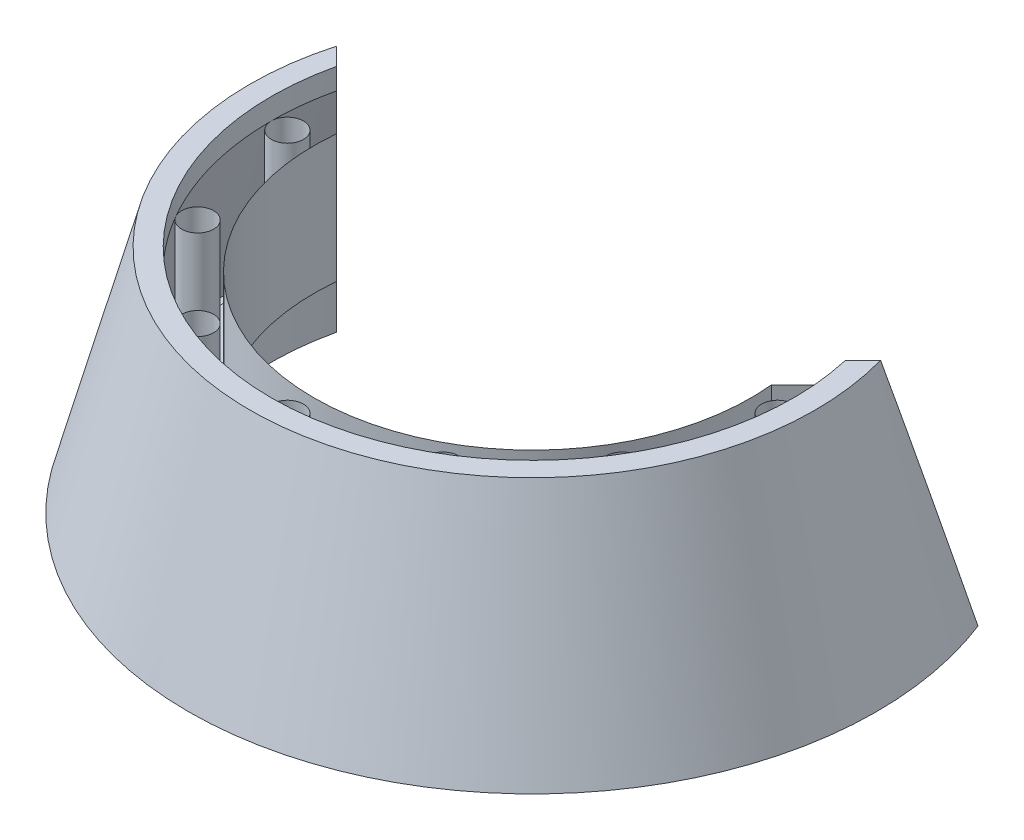
SolidWorks part; units mm, degrees
material "PLA/ABS"
ref_plane "Front Plane" through (0, 0, 0) normal (0, 0, 1) x (1, 0, 0)
ref_plane "Top Plane" through (0, 0, 0) normal (0, 1, 0) x (1, 0, 0)
ref_plane "Right Plane" through (0, 0, 0) normal (1, 0, 0) x (0, 0, -1)
other "Bounding Box"
ref_plane "Default Plane" through (-8.9266, -12.7485, 0) normal (-0.1736, 0.9848, 0) x (0.9848, 0.1736, 0)
sketch "Sketch1" plane through (0, 0, 0) normal (1, 0, 0) x (0, 0, -1)
  line L0 (0, 0) -> (77.7875, 0) construction
  line L1 (65.0875, -19.05) -> (65.0875, 19.05)
  line L2 (65.0875, 19.05) -> (77.7875, 19.05)
  line L3 (77.7875, 19.05) -> (77.7875, 25.4)
  line L4 (77.7875, 25.4) -> (84.1375, 25.4)
  line L5 (84.1375, 25.4) -> (102.5135, -43.18)
  line L6 (102.5135, -43.18) -> (77.7875, -43.18)
  line L7 (77.7875, -43.18) -> (77.7875, -25.4)
  line L9 (77.7875, -25.4) -> (77.7875, -19.05)
  line L10 (77.7875, -19.05) -> (65.0875, -19.05)
  line L11 (-151.3417, -44.45) -> (364.2967, -44.45) construction
  line L12 (0, -44.45) -> (0, 0) construction
  line L13 (77.7875, -19.05) -> (77.7875, 19.05) construction
  point P17 (0, 0)
  point P18 (65.6727, -25.4)
  point P19 (0, 0)
  point P20 (76.5067, -25.4)
  point P21 (74.7714, -25.4)
  point P22 (76.2, -25.4)
  point P23 (78.7296, -25.4)
  dimension "D1" = 77.7875
  dimension "D2" = 75
  dimension "D3" = 12.7
  dimension "D4" = 44.45
  dimension "D5" = 38.1
  dimension "D6" = 6.35
  dimension "D7" = 1.27
  dimension "D9" = 6.35
revolve "Revolve1" add sketch "Sketch1" angle 360 about L12
sketch "Sketch2" plane through (0, 19.05, 0) normal (0, 1, 0) x (1, 0, 0)
  line L0 (0, 0) -> (0, -73.025) construction
  circle A0 centre (0, -73.025) radius 4.7625
  circle A1 centre (0, 0) radius 77.7875 construction
  dimension "D1" = 9.525
extrude "Cut-Extrude1" cut sketch "Sketch2" against normal through all
pattern_circular "CirPattern1" count 12 over 360 about axis through (0, 0, 0) along (0, 1, 0) of "Cut-Extrude1"
sketch "Sketch3" plane through (0, 0, 0) normal (0, 1, 0) x (1, 0, 0)
  line L0 (0, 0) -> (183.5524, 183.5524) construction
  line L1 (0, 0) -> (-197.1438, 197.1438) construction
  line L2 (0, 0) -> (0, 94.8014) construction
  line L3 (0, -58.3717) -> (95.5386, 37.1669)
  line L4 (0, -58.3717) -> (-95.5386, 37.1669)
  circle A0 centre (0, 0) radius 102.5135 construction
  arc A1 (-95.5386, 37.1669) -> (95.5386, 37.1669) centre (0, 0) cw
  point P9 (0, -54.9417)
  point P15 (178.4999, 98.1074)
  dimension "D1" = 45
  dimension "D2" = 41.275
extrude "Cut-Extrude2" cut sketch "Sketch3" against normal through all both and the other way through all
